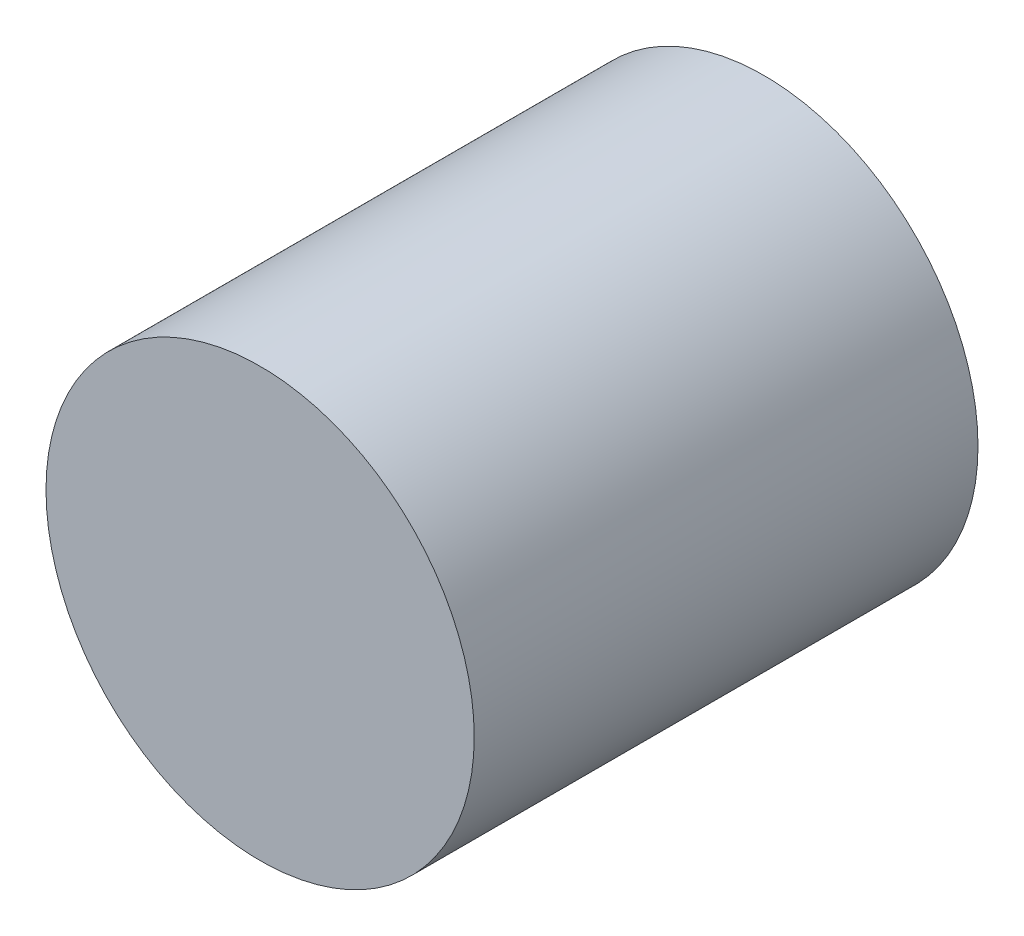
SolidWorks part; units mm, degrees
ref_plane "Спереди" through (0, 0, 0) normal (0, 0, 1) x (1, 0, 0)
ref_plane "Сверху" through (0, 0, 0) normal (0, 1, 0) x (1, 0, 0)
ref_plane "Справа" through (0, 0, 0) normal (1, 0, 0) x (0, 0, -1)
sketch "Эскиз1" plane through (0, 0, 0) normal (0, 0, 1) x (1, 0, 0)
  circle A0 centre (0, 0) radius 8.5
  dimension "D1" = 17
extrude "Бобышка-Вытянуть1" add sketch "Эскиз1" along normal blind 20
